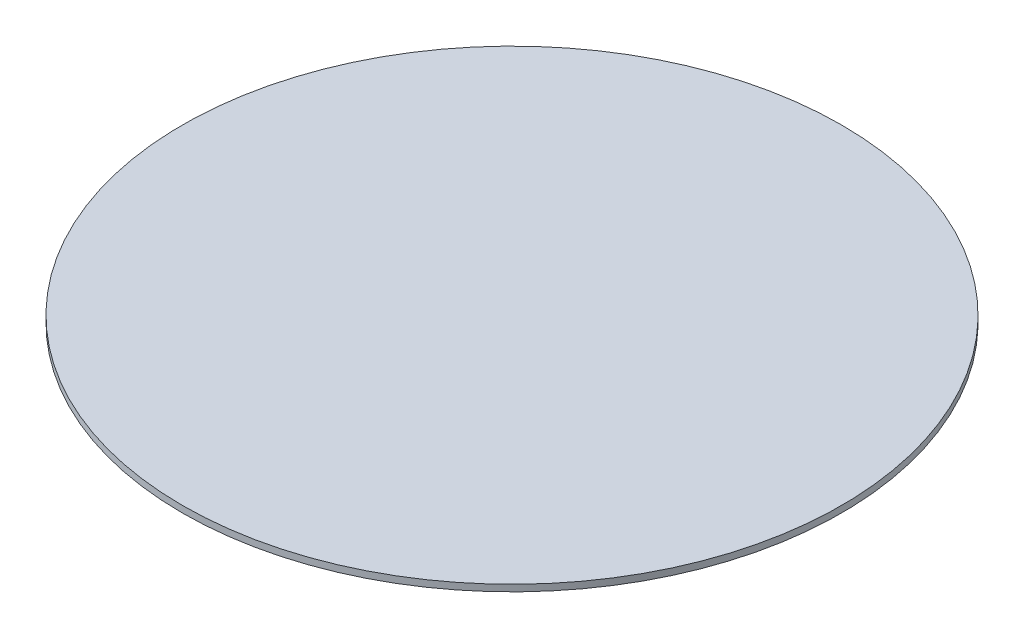
SolidWorks part; units mm, degrees
ref_plane "Ebene vorne" through (0, 0, 0) normal (0, 0, 1) x (1, 0, 0)
ref_plane "Ebene oben" through (0, 0, 0) normal (0, 1, 0) x (1, 0, 0)
ref_plane "Ebene rechts" through (0, 0, 0) normal (1, 0, 0) x (0, 0, -1)
sketch "Skizze1" plane through (0, 0, 0) normal (0, 1, 0) x (1, 0, 0)
  circle A0 centre (0, 0) radius 600
  dimension "Breite" = 1200
extrude "Aufsatz-Linear austragen1" add sketch "Skizze1" along normal blind 12
